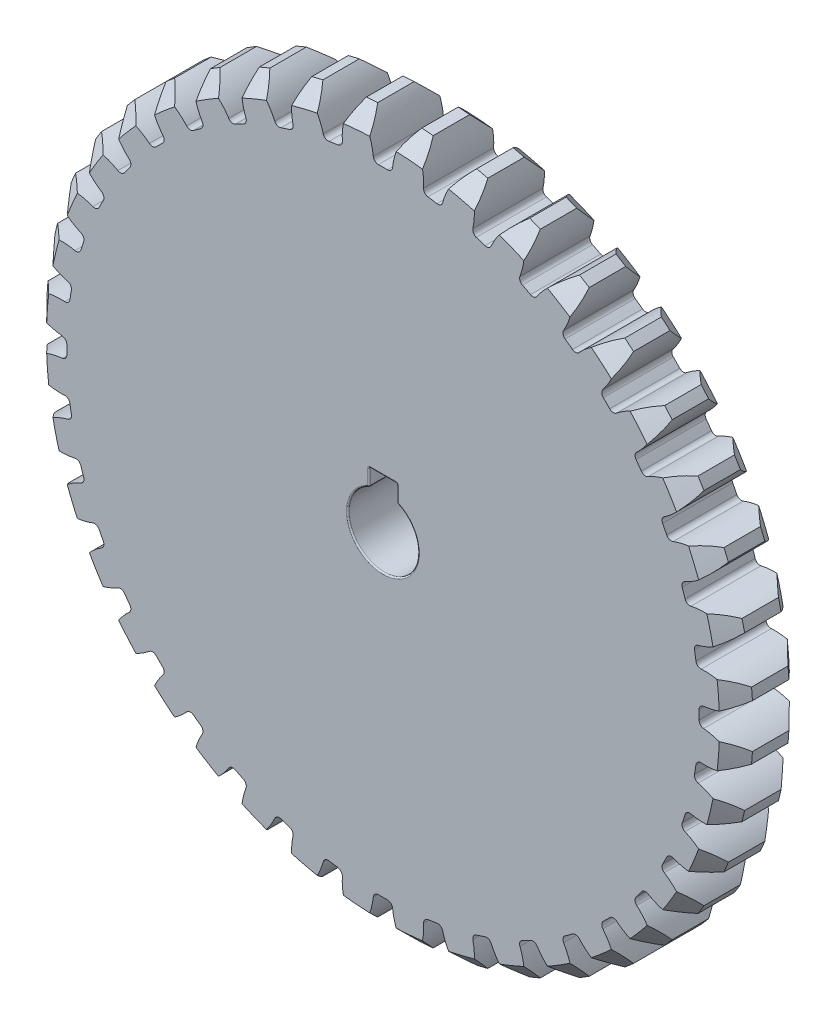
SolidWorks part; units mm, degrees
ref_plane "Front Plane" through (0, 0, 0) normal (0, 0, 1) x (1, 0, 0)
ref_plane "Top Plane" through (0, 0, 0) normal (0, 1, 0) x (1, 0, 0)
ref_plane "Right Plane" through (0, 0, 0) normal (1, 0, 0) x (0, 0, -1)
sketch "Sketch1" plane through (0, 0, 0) normal (0, 0, 1) x (1, 0, 0)
  circle A0 centre (0, 0) radius 48 construction
  circle A1 centre (0, 0) radius 50.4
  dimension "D1" = 96
  dimension "D2" = 100.8
extrude "Boss-Extrude1" add sketch "Sketch1" along normal mid plane 10
sketch "Sketch2" plane through (0, 0, 0) normal (0, 0, 1) x (1, 0, 0)
  line L0 (0, 0) -> (0, 50.4) construction
  line L1 (0, 0) -> (7.8843, 49.7795) construction
  line L2 (0, 0) -> (3.9543, 50.2446) construction
  line L3 (-1.3322, 45.0803) -> (0, 0) construction
  line L4 (-1.8845, 47.963) -> (1.8845, 47.963) construction
  line L5 (1.8845, 47.963) -> (5.6418, 47.6673) construction
  line L6 (-2.7443, 50.3252) -> (0, 42.7855) construction
  circle A0 centre (0, 0) radius 45.6 construction
  circle A2 centre (0, 0) radius 50.4 construction
  arc A3 (-3.1426, 50.3019) -> (-1.3322, 45.0803) centre (-10.5532, 44.8078) cw
  circle A4 centre (0, 0) radius 50.4 construction
  arc A5 (3.1426, 50.3019) -> (1.3322, 45.0803) centre (10.5532, 44.8078) ccw
  circle A6 centre (0, 0) radius 48 construction
  arc A7 (1.3322, 45.0803) -> (-1.3322, 45.0803) centre (0, 0) ccw
  arc A8 (3.1426, 50.3019) -> (-3.1426, 50.3019) centre (0, 0) ccw
  dimension "D1" = 9
  dimension "D2" = 4.8
  dimension "D4" = 20
  dimension "D3" = 0.5
extrude "Cut-Extrude1" cut sketch "Sketch2" against normal through all both and the other way through all contours A5 A8 A3 A7
fillet "Fillet1" radius 0.72 2 edges at (1.3322, 45.0803, 0) (-1.3322, 45.0803, 0)
chamfer "Chamfer1" distance 2.4 angle 45 2 edges at (0, -50.4, -5) (0, -50.4, 5)
pattern_circular "CirPattern1" count 40 over 360 about axis through (0, 0, 0) along (0, 0, 1) of "Fillet1", "Cut-Extrude1"
sketch "Sketch3" plane through (0, 0, 5) normal (0, 0, 1) x (1, 0, 0)
  line L2 (-2, 4.5826) -> (-2, 7)
  line L3 (-2, 7) -> (2, 7)
  line L4 (2, 4.5826) -> (2, 7)
  arc A0 (-2, 4.5826) -> (2, 4.5826) centre (0, 0) ccw
  point P3 (0, 5)
  point P5 (0, 7)
  dimension "D1" = 10
  dimension "D2" = 2
  dimension "D3" = 4
extrude "Cut-Extrude2" cut sketch "Sketch3" against normal through all
fillet "Fillet2" radius 0.2 12 edges at (0, -5, 5) (0, -5, -5) (-2, 4.5826, 0) (2, 4.5826, 0) (0, 7, -5) (0, 7, 5) (-2, 7, 0) (-2, 5.7913, -5) (-2, 5.7913, 5) (2, 5.7913, -5) (2, 7, 0) (2, 5.7913, 5)
sketch "Sketch4" plane through (0, 0, 0) normal (0, 0, 1) x (1, 0, 0)
  circle A0 centre (0, 0) radius 48
equation "\"Module\"= 2.4"
equation "\"Number of Teeth\"= 40'Number of Teeth"
equation "\"Pressure Angle\"= 20"
equation "\"D1@Sketch1\"=\"Module\" * \"Number of Teeth\""
equation "\"D2@Sketch1\"=( \"Number of Teeth\" + 2) * \"Module\""
equation "\"D1@Sketch2\"=360 / \"Number of Teeth\""
equation "\"D2@Sketch2\"= \"Module\" * 2"
equation "\"D4@Sketch2\"=\"Pressure Angle\""
equation "\"D1@Fillet1\"=0.3 * \"Module\""
equation "\"D1@CirPattern1\"= \"Number of Teeth\""
equation "\"D1@Chamfer1\"= \"Module\""
equation "\"Gear Thickness\"= 10"
equation "\"D1@Boss-Extrude1\"= \"Gear Thickness\""
